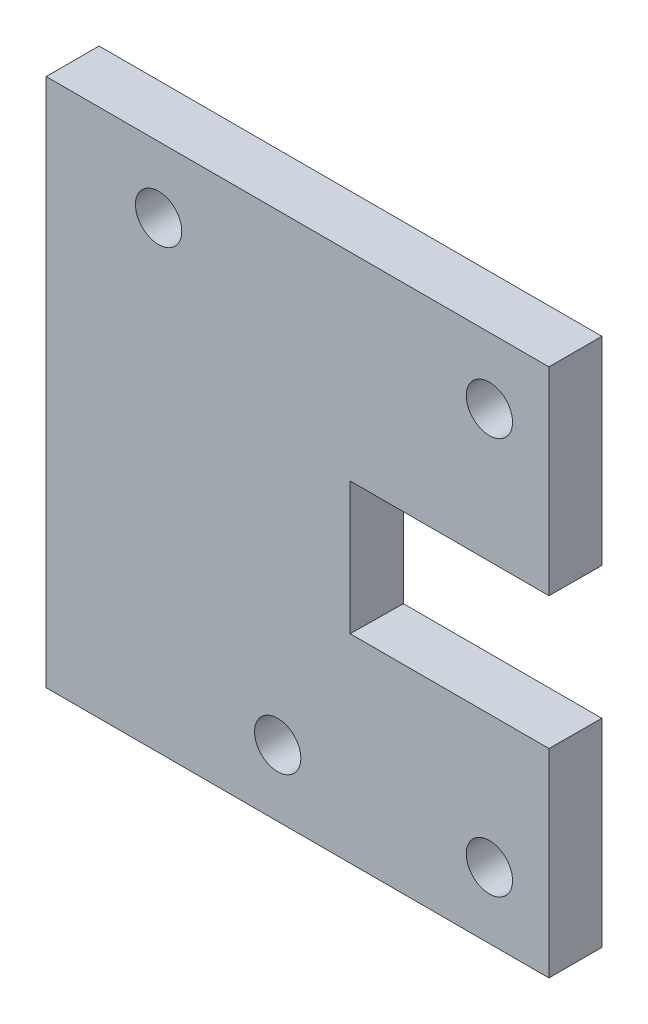
SolidWorks part; units mm, degrees
ref_plane "前视基准面" through (0, 0, 0) normal (0, 0, 1) x (1, 0, 0)
ref_plane "上视基准面" through (0, 0, 0) normal (0, 1, 0) x (1, 0, 0)
ref_plane "右视基准面" through (0, 0, 0) normal (1, 0, 0) x (0, 0, -1)
sketch "草图1" plane through (0, 0, 0) normal (0, 0, 1) x (1, 0, 0)
  line L1 (25, -20) -> (-25, -20)
  line L2 (25, -20) -> (25, 20)
  line L3 (25, 20) -> (-25, 20)
  line L4 (-25, -20) -> (-25, 20)
  line L5 (25, -20) -> (-25, 20) construction
  line L6 (25, 20) -> (-25, -20) construction
  point P0 (0, 0)
  point P6 (0, 0)
  point P7 (0, 0)
  dimension "D1" = 50
  dimension "D2" = 40
extrude "凸台-拉伸1" add sketch "草图1" along normal blind 4
sketch "草图2" plane through (0, 0, 4) normal (0, 0, 1) x (1, 0, 0)
  line L0 (-25, 20) -> (-25, -20) construction
  line L1 (20.5, -15) -> (-20.5, -15) construction
  line L2 (20.5, -15) -> (20.5, 15) construction
  line L3 (20.5, 15) -> (-20.5, 15) construction
  line L4 (-20.5, -15) -> (-20.5, 15) construction
  line L5 (20.5, -15) -> (-20.5, 15) construction
  line L6 (20.5, 15) -> (-20.5, -15) construction
  line L7 (25, 20) -> (-25, 20) construction
  circle A0 centre (-20.5, 15) radius 1.75
  circle A1 centre (-4.5, 15) radius 1.75
  circle A2 centre (20.5, 15) radius 1.75
  circle A3 centre (20.5, -15) radius 1.75
  circle A4 centre (4.5, -15) radius 1.75
  circle A5 centre (-20.5, -15) radius 1.75
  point P0 (0, 0)
  dimension "D3" = 3.5
  dimension "D5" = 25
  dimension "D1" = 4.5
  dimension "D2" = 5
  dimension "D4" = 25
extrude "切除-拉伸1" cut sketch "草图2" against normal blind 4
sketch "草图3" plane through (-25, 0, 0) normal (-1, 0, 0) x (0, 0, 1)
  line L4 (0, 20) -> (0, -20)
  line L5 (0, -20) -> (4, -20)
  line L6 (4, -20) -> (4, 20)
  line L7 (4, 20) -> (0, 20)
  line L8 (0, 20) -> (0, -20)
  line L9 (0, -20) -> (4, -20)
  line L10 (4, -20) -> (4, 20)
  line L11 (4, 20) -> (0, 20)
  dimension "D1" = 0
extrude "切除-拉伸2" cut sketch "草图3" against normal blind 12
sketch "草图8" plane through (0, 0, 0) normal (0, 0, 1) x (1, 0, 0)
  line L10 (26, 5) -> (10, 5)
  line L11 (26, 5) -> (26, -5)
  line L12 (26, -5) -> (10, -5)
  line L13 (10, 5) -> (10, -5)
  point P4 (0, 0)
  point P5 (0, 0)
  point P6 (0, 0)
  point P7 (0, 0)
  point P8 (0, 0)
  point P9 (0, 0)
  point P10 (0, 0)
  point P11 (0, 0)
  point P12 (0, 0)
  point P13 (0, 0)
  point P14 (0, 0)
  point P15 (0, 0)
sketch "草图11" plane through (0, 0, 4) normal (0, 0, 1) x (1, 0, 0)
  line L1 (9.9726, 5.0204) -> (25.9726, 5.0204)
  line L2 (9.9726, 5.0204) -> (9.9726, -4.9796)
  line L3 (9.9726, -4.9796) -> (25.9726, -4.9796)
  line L4 (25.9726, 5.0204) -> (25.9726, -4.9796)
  point P4 (0, 0)
  point P5 (0, 0)
  point P6 (0, 0)
  point P7 (0, 0)
  point P8 (0, 0)
  point P9 (0, 0)
  point P10 (0, 0)
  point P11 (0, 0)
loft "切除-放样5" cut profiles "草图8", "草图11"
